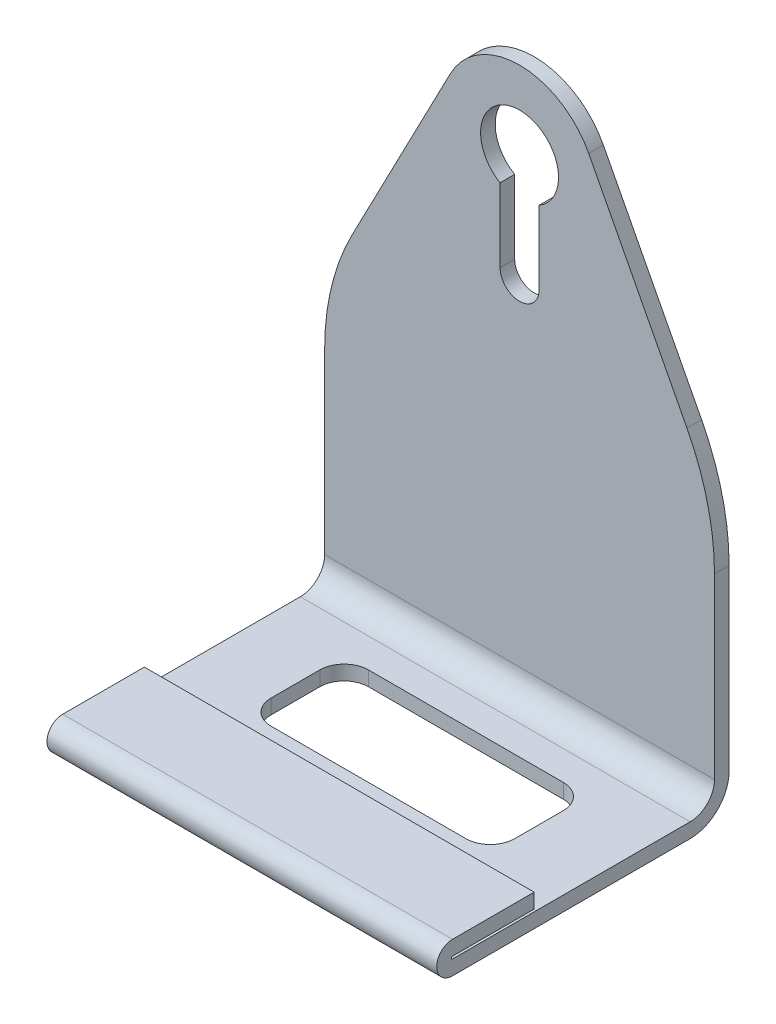
SolidWorks part; units mm, degrees
material "Plain Carbon Steel"
ref_plane "Front Plane" through (0, 0, 0) normal (1, 0, 0) x (0, 1, 0)
ref_plane "Top Plane" through (0, 0, 0) normal (0, 0, 1) x (0, 1, 0)
ref_plane "Right Plane" through (0, 0, 0) normal (0, 1, 0) x (-1, 0, 0)
sketch "Sketch1" plane through (0, 0, 0) normal (1, 0, 0) x (0, 1, 0)
  line L0 (8, 0) -> (115, 0)
  line L2 (115, 3) -> (8, 3)
  line L3 (3, 8) -> (3, 56.75)
  line L4 (3.5, 56.75) -> (3.5, 40)
  line L5 (3.5, 40) -> (6.5, 40)
  line L6 (6.5, 40) -> (6.5, 56.75)
  line L7 (0, 56.75) -> (0, 8)
  line L8 (115, 0) -> (115, 3)
  arc A0 (3, 56.75) -> (3.5, 56.75) centre (3.25, 56.75) cw
  arc A1 (6.5, 56.75) -> (0, 56.75) centre (3.25, 56.75) ccw
  arc A2 (8, 0) -> (0, 8) centre (8, 8) cw
  arc A3 (8, 3) -> (3, 8) centre (8, 8) cw
  point P13 (3.25, 60)
  point P16 (0, 0)
  dimension "D4" = 3
  dimension "D5" = 6.5
  dimension "D7" = 8
  dimension "D8" = 5
  dimension "D1" = 115
  dimension "D2" = 3
  dimension "D3" = 60
  dimension "D6" = 20
extrude "Boss-Extrude1" add sketch "Sketch1" along normal mid plane 80
sketch "Sketch2" plane through (0, 0, 3) normal (0, 0, 1) x (1, 0, 0)
  line L0 (40, 115) -> (-40, 115) construction
  line L1 (-40, 56.8116) -> (-14.1922, 106.388)
  line L3 (40, 115) -> (40, 8) construction
  line L4 (14.1922, 106.388) -> (40, 56.8116)
  line L6 (-40, 115) -> (-40, 8) construction
  arc A0 (14.1922, 106.388) -> (-14.1922, 106.388) centre (0, 99) ccw
  point P12 (40, 56.533)
  dimension "D1" = 16
  dimension "D2" = 55
extrude "Cut-Extrude2" cut sketch "Sketch2" against normal through all both and the other way through all
fillet "Fillet2" radius 50 2 edges at (40, 56.8116, 1.5) (-40, 56.8116, 1.5)
sketch "Sketch4" plane through (0, 0, 3) normal (0, 0, 1) x (1, 0, 0)
  line L0 (0, 99) -> (0, 77) construction
  line L2 (4, 99) -> (4, 77)
  line L3 (-4, 99) -> (-4, 77)
  circle A0 centre (0, 99) radius 8
  arc A1 (14.1922, 106.388) -> (-14.1922, 106.388) centre (0, 99) ccw construction
  arc A2 (4, 99) -> (-4, 99) centre (0, 99) ccw
  arc A3 (-4, 77) -> (4, 77) centre (0, 77) ccw
  point P9 (0, 88)
  dimension "D1" = 16
  dimension "D2" = 22
  dimension "D3" = 8
extrude "Cut-Extrude4" cut sketch "Sketch4" against normal through all both and the other way through all
sketch "Sketch5" plane through (0, 3, 0) normal (0, 1, 0) x (-1, 0, 0)
  line L1 (-20, 14) -> (20, 14)
  line L2 (-25, 19) -> (-25, 29)
  line L3 (-20, 34) -> (20, 34)
  line L4 (25, 19) -> (25, 29)
  line L5 (-25, 14) -> (25, 34) construction
  line L6 (-25, 34) -> (25, 14) construction
  arc A0 (-20, 14) -> (-25, 19) centre (-20, 19) cw
  arc A1 (20, 14) -> (25, 19) centre (20, 19) ccw
  arc A2 (20, 34) -> (25, 29) centre (20, 29) cw
  arc A3 (-25, 29) -> (-20, 34) centre (-20, 29) cw
  point P0 (0, 24)
  dimension "D4" = 5
  dimension "D1" = 20
  dimension "D2" = 50
  dimension "D3" = 14
extrude "Cut-Extrude5" cut sketch "Sketch5" against normal through all both and the other way through all
